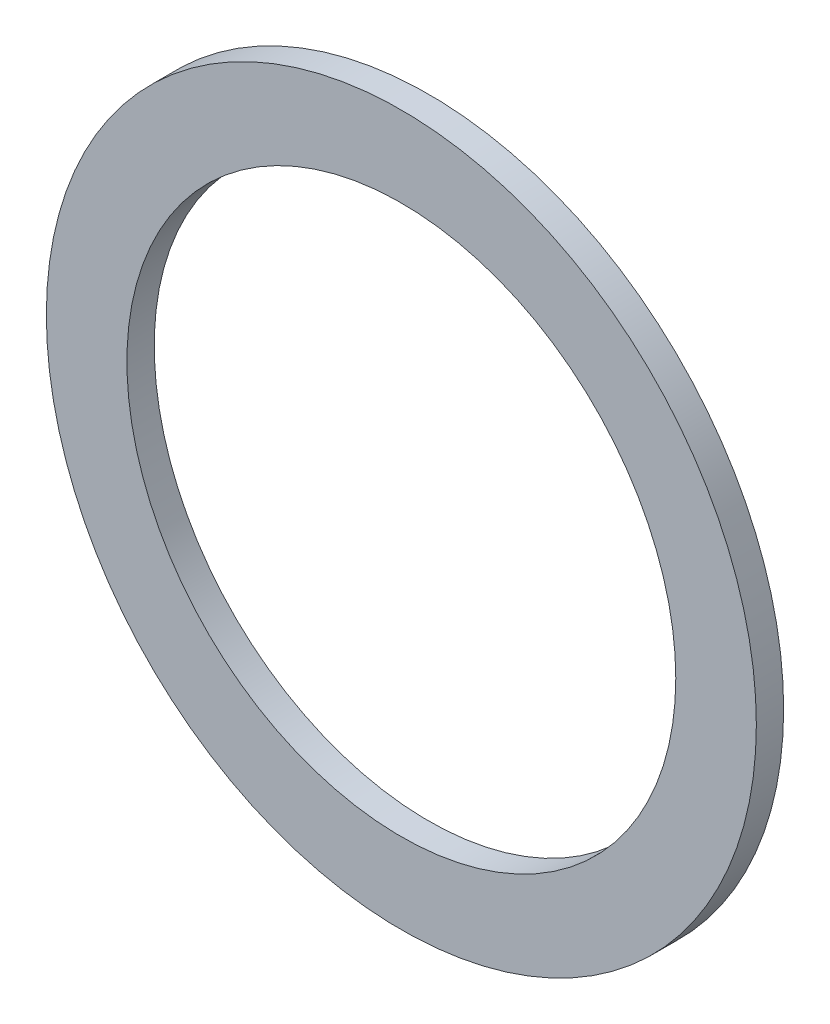
SolidWorks part; units mm, degrees
ref_plane "正面" through (0, 0, 0) normal (1, 0, 0) x (0, 1, 0)
ref_plane "平面" through (0, 0, 0) normal (0, 0, 1) x (0, 1, 0)
ref_plane "右側面" through (0, 0, 0) normal (0, 1, 0) x (-1, 0, 0)
sketch "ｽｹｯﾁ1" plane through (0, 0, 0) normal (0, 0, 1) x (0, 1, 0)
  circle A0 centre (0, 0) radius 6.5
  circle A1 centre (0, 0) radius 5.025
  dimension "D1" = 10.05
  dimension "D2" = 13
extrude "ﾎﾞｽ - 押し出し1" add sketch "ｽｹｯﾁ1" along normal blind 0.5
